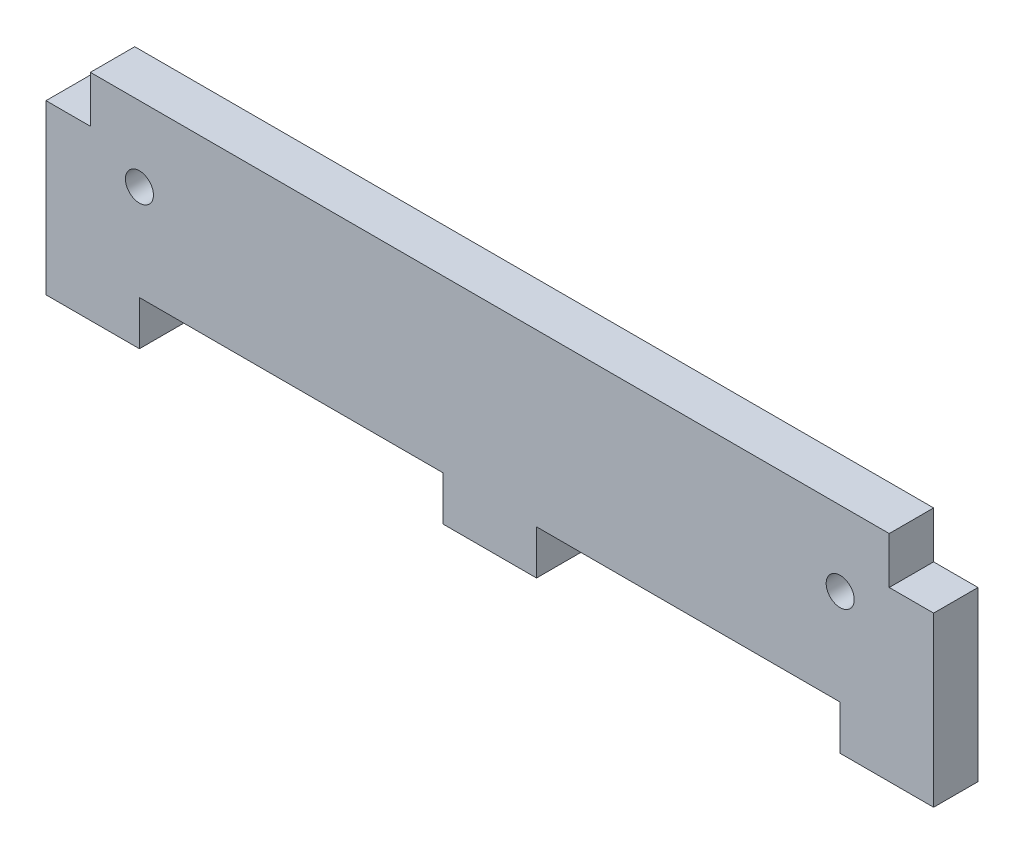
SolidWorks part; units mm, degrees
material "Pine"
ref_plane "Front Plane" through (0, 0, 0) normal (0, 0, 1) x (1, 0, 0)
ref_plane "Top Plane" through (0, 0, 0) normal (0, 1, 0) x (1, 0, 0)
ref_plane "Right Plane" through (0, 0, 0) normal (1, 0, 0) x (0, 0, -1)
sketch "Sketch1" plane through (0, 0, 0) normal (0, 0, 1) x (1, 0, 0)
  line L1 (0, 0) -> (95, 0)
  line L2 (0, 0) -> (0, 23)
  line L3 (0, 23) -> (95, 23)
  line L4 (95, 0) -> (95, 23)
  dimension "D1" = 23
  dimension "D2" = 95
extrude "Boss-Extrude1" add sketch "Sketch1" along normal blind 4.75
sketch "Sketch2" plane through (0, 0, 4.75) normal (0, 0, 1) x (1, 0, 0)
  line L0 (0, 0) -> (95, 0) construction
  line L1 (10, 0) -> (42.5, 0)
  line L2 (10, 0) -> (10, 4.75)
  line L3 (10, 4.75) -> (42.5, 4.75)
  line L4 (42.5, 0) -> (42.5, 4.75)
  line L5 (0, 23) -> (0, 0) construction
  line L6 (52.5, 0) -> (85, 0)
  line L7 (52.5, 0) -> (52.5, 4.75)
  line L8 (52.5, 4.75) -> (85, 4.75)
  line L9 (85, 0) -> (85, 4.75)
  line L10 (95, 0) -> (95, 23) construction
  dimension "D1" = 10
  dimension "D2" = 4.75
  dimension "D3" = 10
  dimension "D4" = 10
extrude "Cut-Extrude1" cut sketch "Sketch2" against normal through all
sketch "Sketch4" plane through (0, 0, 4.75) normal (0, 0, 1) x (1, 0, 0)
  line L0 (95, 23) -> (0, 23) construction
  line L1 (0, 23) -> (0, 0) construction
  line L2 (95, 0) -> (95, 23) construction
  circle A0 centre (10, 15) radius 1.5
  circle A1 centre (85, 15) radius 1.5
  dimension "D1" = 3
  dimension "D4" = 8
  dimension "D5" = 10
  dimension "D2" = 8
  dimension "D3" = 10
extrude "Cut-Extrude2" cut sketch "Sketch4" against normal through all
sketch "Sketch5" plane through (0, 0, 4.75) normal (0, 0, 1) x (1, 0, 0)
  line L1 (0, 23) -> (4.75, 23)
  line L2 (0, 23) -> (0, 18)
  line L3 (0, 18) -> (4.75, 18)
  line L4 (4.75, 23) -> (4.75, 18)
  line L5 (95, 23) -> (90.25, 23)
  line L6 (95, 23) -> (95, 18)
  line L7 (95, 18) -> (90.25, 18)
  line L8 (90.25, 23) -> (90.25, 18)
  dimension "D1" = 4.75
  dimension "D2" = 5
extrude "Cut-Extrude3" cut sketch "Sketch5" against normal through all
